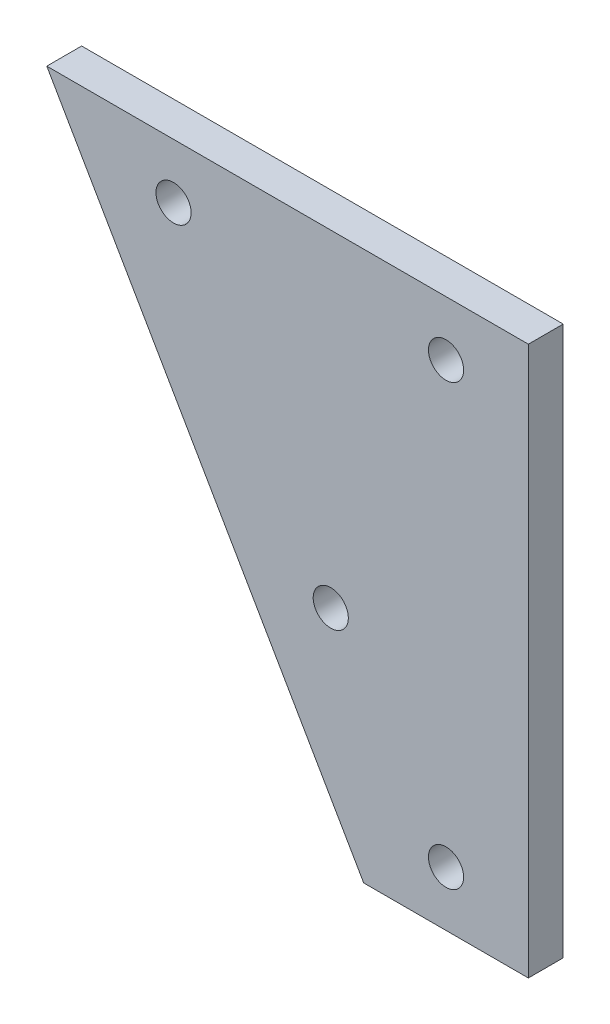
SolidWorks part; units mm, degrees
ref_plane "Front Plane" through (0, 0, 0) normal (0, 0, 1) x (1, 0, 0)
ref_plane "Top Plane" through (0, 0, 0) normal (0, 1, 0) x (1, 0, 0)
ref_plane "Right Plane" through (0, 0, 0) normal (1, 0, 0) x (0, 0, -1)
sketch "Sketch1" plane through (0, 0, 0) normal (0, 0, 1) x (1, 0, 0)
  line L0 (0, 0) -> (43.8675, 0)
  line L2 (28.8675, -50) -> (0, 0)
  line L3 (43.8675, 0) -> (43.8675, -50)
  line L4 (43.8675, -50) -> (28.8675, -50)
  line L5 (28.8675, -50) -> (28.8675, 0) construction
  line L6 (28.8675, -20) -> (17.3205, 0) construction
  line L7 (8.6603, 0) -> (28.8675, -35) construction
  line L8 (36.3675, 0) -> (36.3675, -50) construction
  circle A0 centre (36.3675, -5) radius 1.6
  circle A1 centre (36.3675, -45) radius 1.6
  circle A2 centre (11.547, -5) radius 1.6
  circle A3 centre (25.8675, -29.8038) radius 1.6
  dimension "D6" = 5
  dimension "D7" = 3.2
  dimension "D8" = 5
  dimension "D9" = 40
  dimension "D1" = 30
  dimension "D2" = 15
  dimension "D3" = 15
  dimension "D4" = 7.5
  dimension "D5" = 7.5
  dimension "D10" = 6
extrude "Boss-Extrude1" add sketch "Sketch1" along normal blind 3.175
